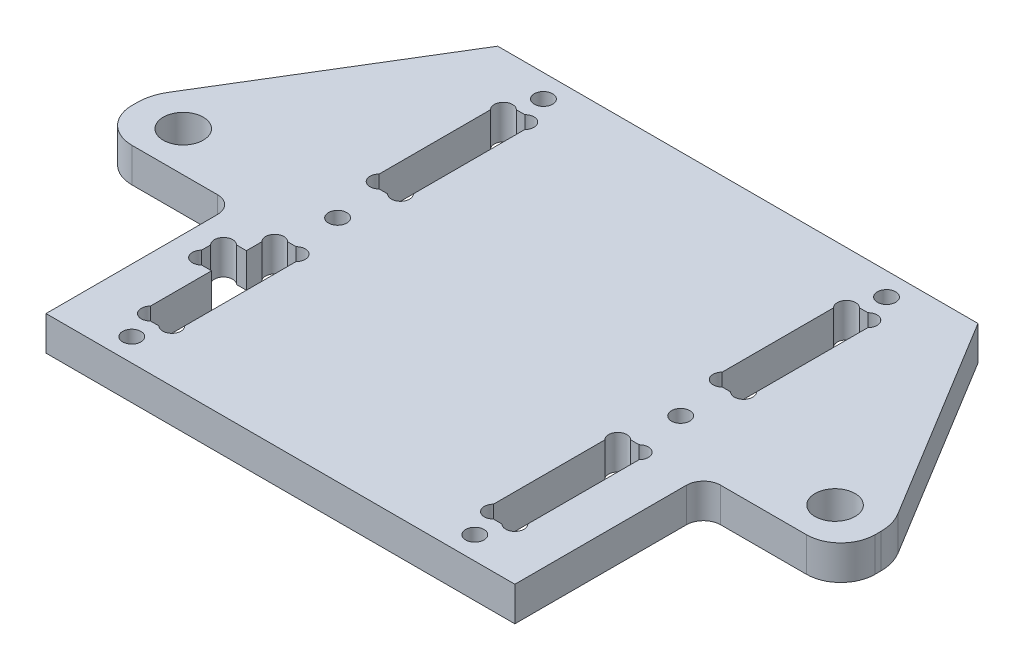
SolidWorks part; units mm, degrees
ref_plane "Plan de face" through (0, 0, 0) normal (0, 0, 1) x (1, 0, 0)
ref_plane "Plan de dessus" through (0, 0, 0) normal (0, 1, 0) x (1, 0, 0)
ref_plane "Plan de droite" through (0, 0, 0) normal (1, 0, 0) x (0, 0, -1)
sketch "Esquisse1" plane through (0, 0, 0) normal (0, 1, 0) x (1, 0, 0)
  line L0 (-116.9557, 0) -> (110.5569, 0) construction
  line L1 (0, -14.338) -> (0, 107.476) construction
  line L2 (-116.9557, 80) -> (110.5569, 80) construction
  line L3 (-65, 95.0623) -> (-65, -11.8265) construction
  line L4 (-33, -11.8265) -> (-33, 88.3991) construction
  line L5 (-111.2655, 40) -> (13.9471, 40) construction
  line L6 (-27, 84.3292) -> (-27, -7.5711) construction
  line L7 (-30, 43.1695) -> (-30, 8.6994) construction
  line L8 (-38.3779, 8) -> (-28.7848, 8) construction
  line L9 (-28.7848, 20) -> (-31.8686, 20) construction
  line L10 (-33, 50.2627) -> (-33, 69.7373)
  line L11 (-42.309, 32) -> (-29.8525, 32) construction
  line L12 (-27, 8) -> (-35.1739, 16.1739) construction
  line L13 (-33, 4) -> (-27, 4) construction
  line L14 (-30.7373, 32) -> (-29.2627, 32)
  line L15 (-33, 29.7373) -> (-33, 27.05)
  line L16 (-30.7373, 8) -> (-29.2627, 8)
  line L17 (-27, 29.7373) -> (-27, 10.2627)
  line L18 (-27, 50.2627) -> (-27, 69.7373)
  line L19 (-30.7373, 48) -> (-29.2627, 48)
  line L20 (-30.7373, 72) -> (-29.2627, 72)
  line L21 (42, 80) -> (63.8321, 44.162)
  line L22 (65, 39) -> (65, 40)
  line L23 (30.7373, 72) -> (29.2627, 72)
  line L24 (30.7373, 48) -> (29.2627, 48)
  line L25 (27, 50.2627) -> (27, 69.7373)
  line L26 (27, 29.7373) -> (27, 10.2627)
  line L27 (-57, 44.7413) -> (-57, 35.4436) construction
  line L28 (-63.8321, 44.162) -> (-42, 80) construction
  line L29 (30.7373, 8) -> (29.2627, 8)
  line L30 (-42, 80) -> (-63.8321, 44.162)
  line L31 (-65, 39) -> (-65, 40)
  line L32 (33, 29.7373) -> (33, 10.2627)
  line L33 (30.7373, 32) -> (29.2627, 32)
  line L34 (33, 50.2627) -> (33, 69.7373)
  line L35 (-42, 80) -> (42, 80)
  line L36 (41, 0) -> (-41, 0)
  line L37 (-74.9954, 33) -> (-10.3063, 33) construction
  line L38 (-41, 0) -> (-41, 30)
  line L39 (-59, 33) -> (-44, 33)
  line L40 (41, 0) -> (41, 30)
  line L41 (59, 33) -> (44, 33)
  line L42 (-43.5505, 24) -> (-18.6263, 24) construction
  line L43 (-69, -15.7297) -> (-69, 36.4985) construction
  line L44 (-45.5, 23.9637) -> (-45.5, -9.1324) construction
  line L45 (-41, -9.1324) -> (-41, 37.5974) construction
  line L46 (-31.1187, 20.95) -> (-38.9416, 20.95) construction
  line L47 (-31.1187, 27.05) -> (-38.9416, 27.05) construction
  line L48 (-37, 28.3928) -> (-37, 19.1751) construction
  line L49 (-37, 27.05) -> (-33.5922, 23.6422) construction
  line L50 (-33, 27.05) -> (-34.7373, 27.05)
  line L51 (-37, 24.7873) -> (-37, 23.2127)
  line L52 (-34.7373, 20.95) -> (-33, 20.95)
  line L53 (-33, 20.95) -> (-33, 10.2627)
  arc A0 (-29.2627, 8) -> (-27, 10.2627) centre (-28.1314, 9.1314) ccw
  arc A1 (-30.7373, 8) -> (-33, 10.2627) centre (-31.8686, 9.1314) cw
  arc A2 (-30.7373, 32) -> (-33, 29.7373) centre (-31.8686, 30.8686) ccw
  arc A3 (-29.2627, 32) -> (-27, 29.7373) centre (-28.1314, 30.8686) cw
  circle A4 centre (-30, 4) radius 1.6
  circle A5 centre (-30, 76) radius 1.6
  arc A6 (-29.2627, 72) -> (-27, 69.7373) centre (-28.1314, 70.8686) cw
  arc A7 (-30.7373, 72) -> (-33, 69.7373) centre (-31.8686, 70.8686) ccw
  arc A8 (-29.2627, 48) -> (-27, 50.2627) centre (-28.1314, 49.1314) ccw
  arc A9 (-30.7373, 48) -> (-33, 50.2627) centre (-31.8686, 49.1314) cw
  circle A10 centre (-30, 40) radius 1.6
  arc A11 (63.8321, 44.162) -> (65, 40) centre (57, 40) cw
  circle A12 centre (57, 40) radius 3.5
  circle A13 centre (30, 4) radius 1.6
  circle A14 centre (30, 40) radius 1.6
  arc A15 (30.7373, 48) -> (33, 50.2627) centre (31.8686, 49.1314) ccw
  arc A16 (-63.8321, 44.162) -> (-65, 40) centre (-57, 40) ccw
  circle A17 centre (-57, 40) radius 3.5
  arc A18 (29.2627, 48) -> (27, 50.2627) centre (28.1314, 49.1314) cw
  arc A19 (30.7373, 72) -> (33, 69.7373) centre (31.8686, 70.8686) cw
  arc A20 (29.2627, 72) -> (27, 69.7373) centre (28.1314, 70.8686) ccw
  circle A21 centre (30, 76) radius 1.6
  arc A22 (29.2627, 32) -> (27, 29.7373) centre (28.1314, 30.8686) ccw
  arc A23 (30.7373, 32) -> (33, 29.7373) centre (31.8686, 30.8686) cw
  arc A24 (30.7373, 8) -> (33, 10.2627) centre (31.8686, 9.1314) ccw
  arc A25 (29.2627, 8) -> (27, 10.2627) centre (28.1314, 9.1314) cw
  arc A27 (-65, 39) -> (-59, 33) centre (-59, 39) ccw
  arc A28 (-44, 33) -> (-41, 30) centre (-44, 30) cw
  arc A29 (44, 33) -> (41, 30) centre (44, 30) ccw
  arc A30 (65, 39) -> (59, 33) centre (59, 39) cw
  arc A31 (-34.7373, 27.05) -> (-37, 24.7873) centre (-35.8686, 25.9186) ccw
  arc A32 (-34.7373, 20.95) -> (-37, 23.2127) centre (-35.8686, 22.0814) cw
  point P108 (-41, 33)
  point P110 (-65, 33)
  dimension "D8" = 8
  dimension "D10" = 3
  dimension "D3" = 6
  dimension "D1" = 6
  dimension "D2" = 3
  dimension "D4" = 24
  dimension "D5" = 12
  dimension "D6" = 4
  dimension "D7" = 45
  dimension "D9" = 8
  dimension "D11" = 36
  dimension "D12" = 23.5
  dimension "D13" = 8
  dimension "D14" = 24
  dimension "D15" = 3.05
  dimension "D16" = 6.1
  dimension "D17" = 4
  dimension "D18" = 45
extrude "Extrusion1" add sketch "Esquisse1" along normal blind 6
